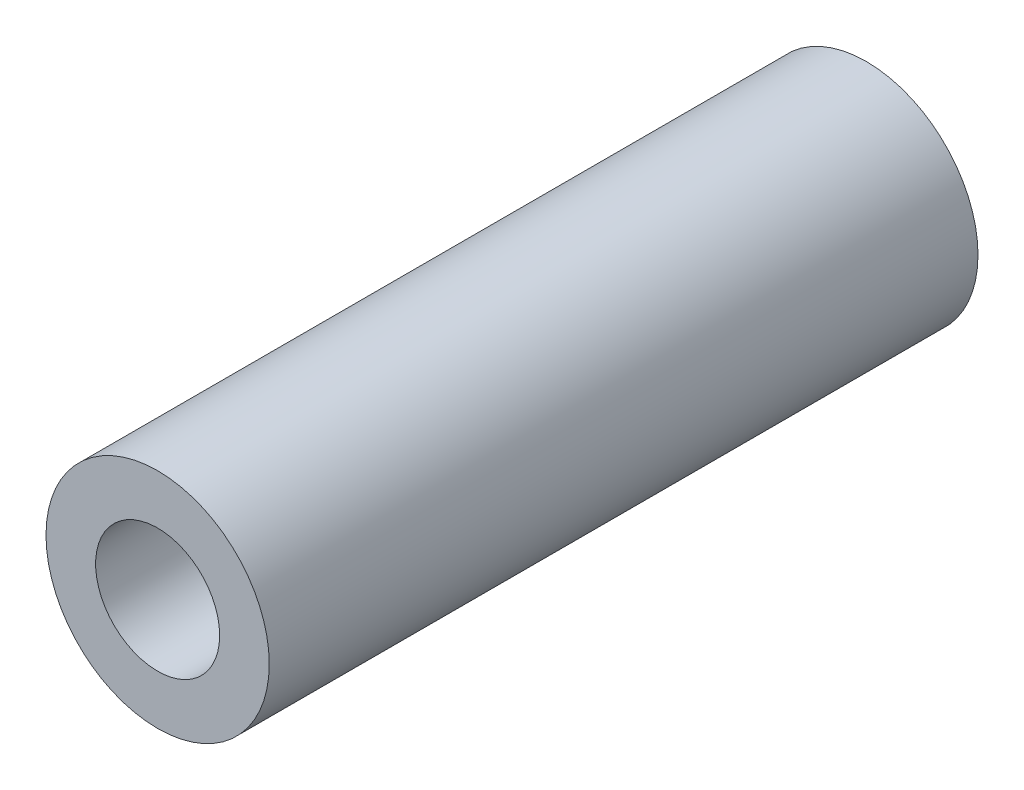
SolidWorks part; units mm, degrees
material "PBT Uniwersalny"
ref_plane "Płaszczyzna przednia" through (0, 0, 0) normal (0, 0, 1) x (1, 0, 0)
ref_plane "Płaszczyzna górna" through (0, 0, 0) normal (0, 1, 0) x (1, 0, 0)
ref_plane "Płaszczyzna prawa" through (0, 0, 0) normal (1, 0, 0) x (0, 0, -1)
sketch "Szkic1" plane through (0, 0, 0) normal (0, 0, 1) x (1, 0, 0)
  circle A1 centre (0, 0) radius 1.75
  circle A2 centre (0, 0) radius 3.15
  dimension "D2" = 3.5
  dimension "D1" = 6.3
extrude "Dodanie-wyciągnięcie1" add sketch "Szkic1" along normal blind 20
